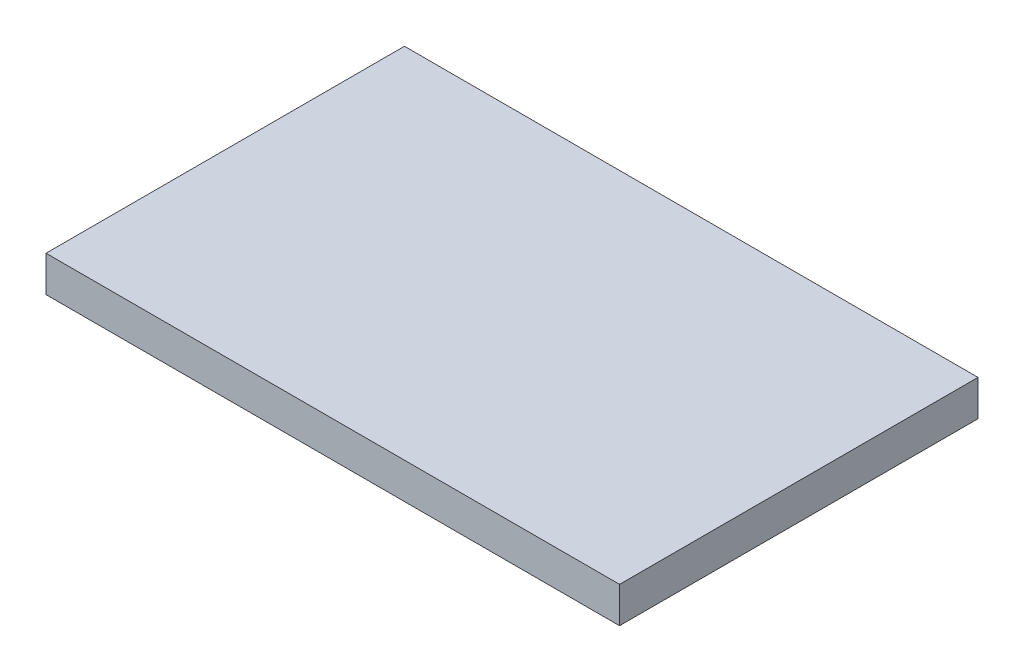
SolidWorks part; units mm, degrees
material "ASTM A36 Steel"
ref_plane "Front Plane" through (0, 0, 0) normal (0, 0, 1) x (1, 0, 0)
ref_plane "Top Plane" through (0, 0, 0) normal (0, 1, 0) x (1, 0, 0)
ref_plane "Right Plane" through (0, 0, 0) normal (1, 0, 0) x (0, 0, -1)
sketch "Sketch1" plane through (0, 0, 0) normal (0, 0, 1) x (1, 0, 0)
  line L0 (0, 0) -> (203.2, 0)
  line L1 (203.2, 0) -> (203.2, -12.7)
  line L2 (203.2, -12.7) -> (0, -12.7)
  line L3 (0, -12.7) -> (0, 0)
  dimension "D1" = 203.2
  dimension "D2" = 12.7
extrude "Boss-Extrude1" add sketch "Sketch1" along normal blind 127
